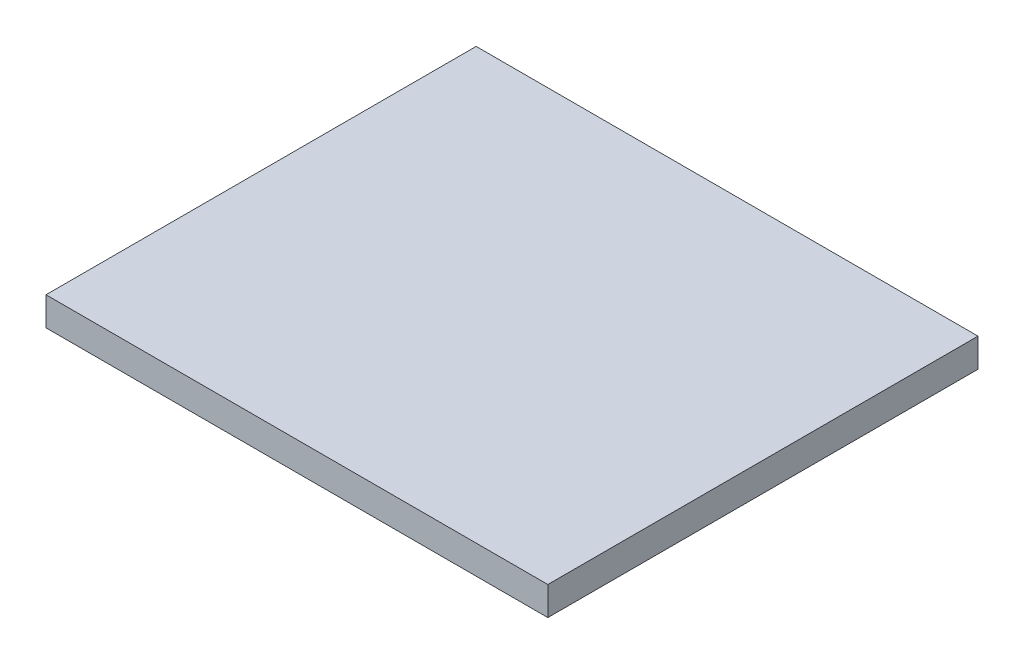
SolidWorks part; units mm, degrees
ref_plane "Front Plane" through (0, 0, 0) normal (0, 0, 1) x (1, 0, 0)
ref_plane "Top Plane" through (0, 0, 0) normal (0, 1, 0) x (1, 0, 0)
ref_plane "Right Plane" through (0, 0, 0) normal (1, 0, 0) x (0, 0, -1)
sketch "Sketch1" plane through (0, 0, 0) normal (0, 1, 0) x (1, 0, 0)
  line L1 (0, 0) -> (175, 0)
  line L2 (0, 0) -> (0, 150)
  line L3 (0, 150) -> (175, 150)
  line L4 (175, 0) -> (175, 150)
  dimension "D1" = 175
  dimension "D2" = 150
extrude "Boss-Extrude2" add sketch "Sketch1" along normal blind 10 contours L2 L3 L4 L1
